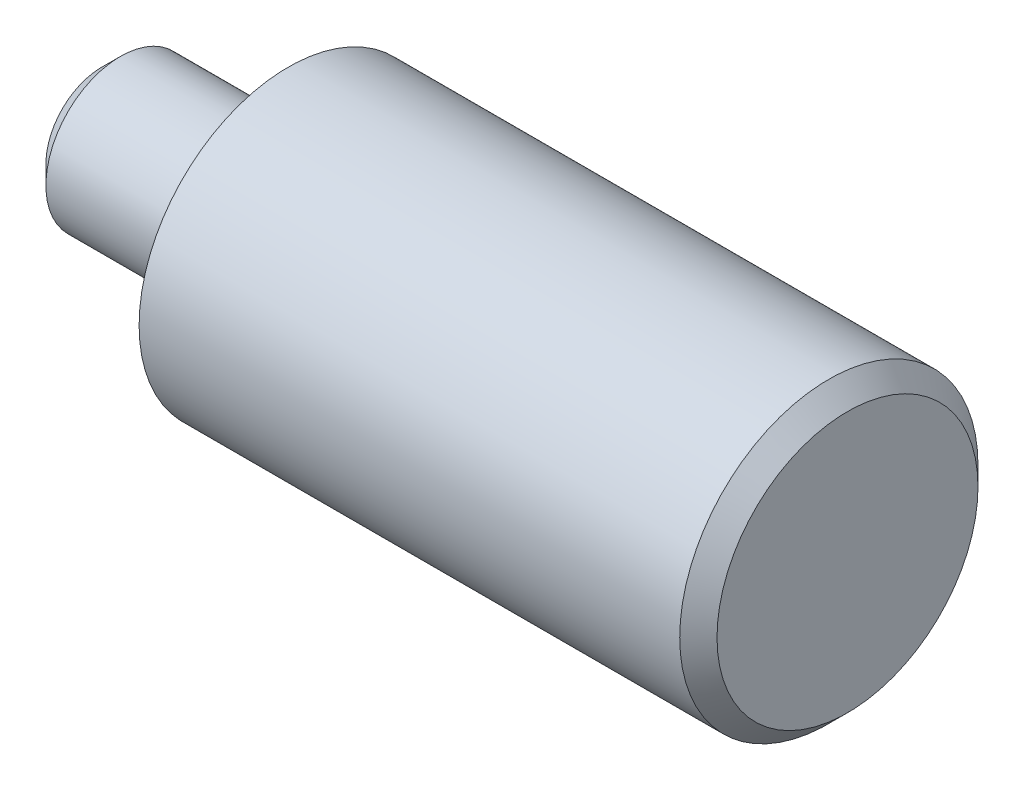
SolidWorks part; units mm, degrees
material "1.0037 (S235JR)"
ref_plane "Front Plane" through (0, 0, 0) normal (0, 0, 1) x (1, 0, 0)
ref_plane "Top Plane" through (0, 0, 0) normal (0, 1, 0) x (1, 0, 0)
ref_plane "Right Plane" through (0, 0, 0) normal (1, 0, 0) x (0, 0, -1)
sketch "Sketch1" plane through (0, 0, 0) normal (0, 0, 1) x (1, 0, 0)
  line L0 (-114.7841, 0) -> (39.5989, 0) construction
  line L1 (0, 0) -> (0, 8)
  line L2 (0, 8) -> (-30, 8)
  line L3 (-30, 8) -> (-30, 4)
  line L4 (-30, 4) -> (-40, 4)
  line L5 (-40, 4) -> (-40, 0)
  line L6 (0, 0) -> (-40, 0)
  point P4 (-37.5926, 0)
  dimension "D1" = 30
  dimension "D2" = 10
  dimension "D3" = 16
  dimension "D4" = 8
revolve "Revolve1" add sketch "Sketch1" angle 360 about L0
cosmetic thread "Cosmetic Thread1" parameters "D1"=10, "D2"=6.891
chamfer "Chamfer1" distance 1 angle 45 2 edges at (0, 0, 8) (-40, 0, 4)
sketch "Sketch2" plane through (0, 0, 0) normal (0, 0, 1) x (1, 0, 0)
  line L0 (0, 0) -> (-49.715, 0) construction
  line L1 (-30, 8) -> (-30, -8) construction
  line L2 (-30, 3) -> (-31, 3)
  line L3 (-30, 3) -> (-30, 4)
  line L4 (-30, 4) -> (-31, 4)
  line L5 (-31, 3) -> (-31, 4)
  line L6 (-30, 4) -> (-39, 4) construction
  dimension "D1" = 1
  dimension "D2" = 1
revolve "Cut-Revolve1" cut sketch "Sketch2" angle 360 about L0
